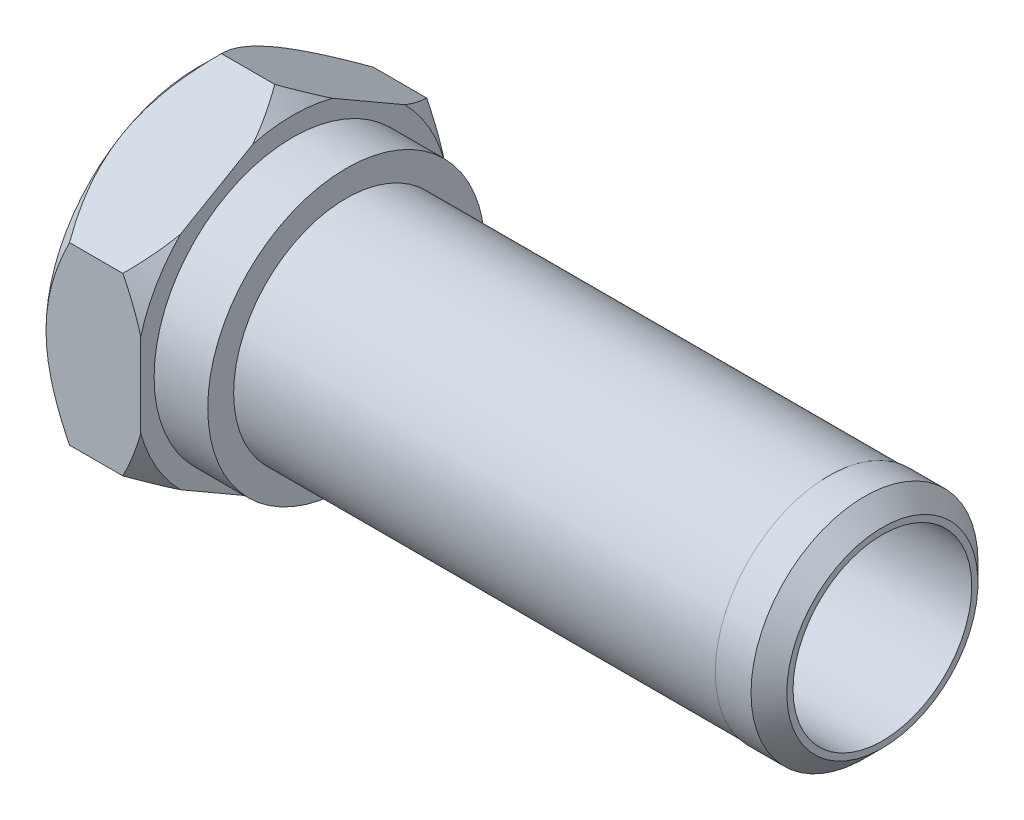
SolidWorks part; units mm, degrees
material "6061-T6 (SS)"
ref_plane "Płaszczyzna XY" through (0, 0, 0) normal (0, 0, 1) x (1, 0, 0)
ref_plane "Płaszczyzna XZ" through (0, 0, 0) normal (0, 1, 0) x (1, 0, 0)
ref_plane "Płaszczyzna YZ" through (0, 0, 0) normal (1, 0, 0) x (0, 0, -1)
sketch "Szkic1" plane through (0, 0, 0) normal (0, 0, 1) x (1, 0, 0)
  line L0 (0, 0) -> (10.2462, 0) construction
  line L1 (0, 5) -> (33, 5)
  line L2 (33, 5) -> (33, 6.35)
  line L3 (33, 6.35) -> (3, 6.35)
  line L4 (3, 6.35) -> (3, 7.75)
  line L5 (3, 7.75) -> (0, 7.75)
  line L6 (0, 7.75) -> (0, 5)
  dimension "D1" = 3
  dimension "D2" = 30
  dimension "D3" = 10
  dimension "D4" = 15.5
  dimension "D5" = 12.7
revolve "Obrót1" add sketch "Szkic1" angle 360 about L0
chamfer "Sfazowanie2" distance 1 angle 45 1 edges at (33, 0, 6.35)
sketch "Szkic2" plane through (0, 0, 0) normal (0, 0, 1) x (1, 0, 0)
  line L0 (3, 7.75) -> (3, 6.35)
  line L1 (3, -6.35) -> (3, -7.75)
  line L2 (3, -6.35) -> (3, -7.75)
  line L3 (3, 7.75) -> (3, 6.35)
  line L4 (33, 5.35) -> (32, 6.35)
  line L5 (32, -6.35) -> (33, -5.35)
  line L6 (32, -6.35) -> (33, -5.35)
  line L7 (33, 5.35) -> (32, 6.35)
  line L8 (3, 0) -> (30.8109, 0) construction
  line L9 (3, 6.35) -> (30, 6.35)
  line L10 (3, 6.35) -> (3, 6.3)
  line L11 (3, 6.3) -> (30, 6.3)
  line L12 (30, 6.35) -> (30, 6.3)
  dimension "D1" = 2
  dimension "D2" = 0.05
revolve "Wycięcie-obrót1" cut sketch "Szkic2" angle 360 about L8
sketch "Szkic3" plane through (0, 0, 0) normal (-1, 0, 0) x (0, 0, 1)
  line L1 (8.5, -4.9075) -> (8.5, 4.9075)
  line L2 (8.5, 4.9075) -> (0, 9.815)
  line L3 (0, 9.815) -> (-8.5, 4.9075)
  line L4 (-8.5, 4.9075) -> (-8.5, -4.9075)
  line L5 (-8.5, -4.9075) -> (0, -9.815)
  line L6 (0, -9.815) -> (8.5, -4.9075)
  circle A0 centre (0, 0) radius 8.5 construction
  circle A1 centre (0, 0) radius 5
  circle A2 centre (0, 0) radius 5 construction
  dimension "D1" = 17
extrude "Dodanie-wyciągnięcie1" add sketch "Szkic3" along normal blind 5.3
sketch "Szkic4" plane through (0, 0, 0) normal (0, 1, 0) x (1, 0, 0)
  line L0 (-5.3, 8.5) -> (-5.3, 12)
  line L1 (-5.3, 12) -> (-1.8, 12)
  line L2 (-1.8, 12) -> (-5.3, 8.5)
  line L3 (0, 0) -> (-4.9952, 0) construction
  dimension "D1" = 45
  dimension "D2" = 12
revolve "Wycięcie-obrót2" cut sketch "Szkic4" angle 360 about L3
sketch "Szkic5" plane through (0, 0, 0) normal (0, 0, 1) x (1, 0, 0)
  line L0 (0, 9.815) -> (0, 7.75)
  line L1 (0, -7.75) -> (0, -9.815)
  line L2 (0, -8.815) -> (0, -9.815)
  line L4 (-1, -9.815) -> (0, -8.815)
  line L5 (-1, -9.815) -> (0, -9.815)
  line L6 (0, 0) -> (10.6319, 0) construction
  dimension "D1" = 45
  dimension "D2" = 1
revolve "Wycięcie-obrót3" cut sketch "Szkic5" angle 360 about L6
chamfer "Sfazowanie3" distance 0.5 angle 45 1 edges at (-5.3, 0, 5)
